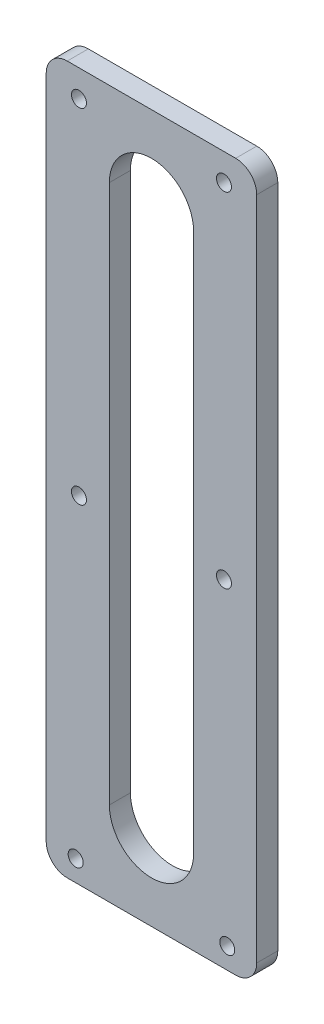
SolidWorks part; units mm, degrees
material "6061-T6 (SS)"
ref_plane "Front Plane" through (0, 0, 0) normal (0, 0, 1) x (1, 0, 0)
ref_plane "Top Plane" through (0, 0, 0) normal (0, 1, 0) x (1, 0, 0)
ref_plane "Right Plane" through (0, 0, 0) normal (1, 0, 0) x (0, 0, -1)
ref_plane "Plane1" through (0, 0, 3.175) normal (0, 0, 1) x (1, 0, 0)
sketch "Sketch1" plane through (0, 0, 3.175) normal (0, 0, 1) x (1, 0, 0)
  line L0 (22.225, 93.98) -> (22.225, 12.7)
  line L1 (9.525, 12.7) -> (9.525, 93.98)
  line L2 (31.75, 0) -> (31.75, 106.68)
  line L3 (31.75, 106.68) -> (0, 106.68)
  line L4 (0, 106.68) -> (0, 0)
  line L5 (0, 0) -> (31.75, 0)
  line L6 (15.875, 0) -> (15.875, 12.7) construction
  arc A0 (9.525, 93.98) -> (22.225, 93.98) centre (15.875, 93.98) cw
  arc A1 (22.225, 12.7) -> (9.525, 12.7) centre (15.875, 12.7) cw
  point P10 (0, 0)
  dimension "D3" = 6.35
  dimension "D1" = 106.68
  dimension "D2" = 31.75
  dimension "D4" = 81.28
  dimension "D5" = 12.7
extrude "Boss-Extrude1" add sketch "Sketch1" against normal blind 3.175
fillet "Fillet1" radius 3.175 4 edges at (31.75, 0, 1.5875) (0, 0, 1.5875) (31.75, 106.68, 1.5875) (0, 106.68, 1.5875)
hole_wizard "#4-40 Tapped Hole1" positions "Sketch3" profile "Sketch2" tap size "#4-40" standard "ANSI Inch" end condition through all
sketch "Sketch3" plane through (0, 0, 0) normal (0, 0, -1) x (-1, 0, 0)
  line L0 (-4.9403, 102.616) -> (-4.9403, 50.8) construction
  line L2 (-4.445, 3.175) -> (-27.305, 3.175) construction
  line L4 (-4.9403, 102.616) -> (-26.8097, 102.616) construction
  line L5 (-26.8097, 102.616) -> (-26.8097, 50.8) construction
  line L6 (-26.8097, 50.8) -> (-4.9403, 50.8) construction
  line L8 (-15.875, 50.8) -> (-15.875, 3.175) construction
  line L14 (-15.875, 3.175) -> (-15.875, 0) construction
  line L15 (-3.175, 0) -> (-28.575, 0) construction
  point P0 (-4.445, 3.175)
  point P1 (-4.9403, 50.8)
  point P2 (-27.305, 3.175)
  point P3 (-26.8097, 50.8)
  point P4 (-26.8097, 102.616)
  point P5 (-4.9403, 102.616)
  dimension "D1" = 21.8694
  dimension "D2" = 51.816
  dimension "D3" = 47.625
  dimension "D4" = 22.86
  dimension "D5" = 3.175
sketch "Sketch2" plane through (4.445, 3.175, 0) normal (1, 0, 0) x (0, 1, 0)
  line L0 (0, 0) -> (0, 3.175)
  line L1 (0, 3.175) -> (1.1303, 3.175)
  line L2 (1.1303, 3.175) -> (1.1303, 0)
  line L5 (1.1303, 0) -> (0, 0)
  line L11 (0, -6.35) -> (0, 107.95) construction
  dimension "Thru Tap Drill Dia." = 2.2606
  dimension "Thru Tap Drill Depth" = 3.175
cosmetic thread "Hole Thread1" parameters "D2"=2.8448
cosmetic thread "Hole Thread2" parameters "D2"=2.8448
cosmetic thread "Hole Thread3" parameters "D2"=2.8448
cosmetic thread "Hole Thread4" parameters "D2"=2.8448
cosmetic thread "Hole Thread5" parameters "D2"=2.8448
cosmetic thread "Hole Thread6" parameters "D2"=2.8448
